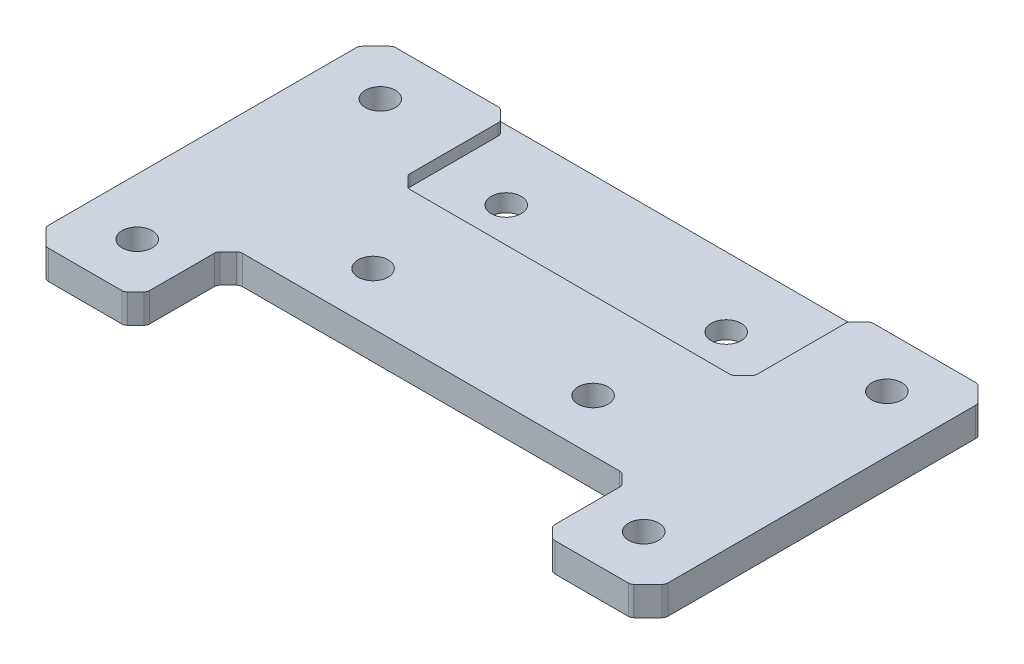
SolidWorks part; units mm, degrees
ref_plane "Front Plane" through (0, 0, 0) normal (0, 0, 1) x (1, 0, 0)
ref_plane "Top Plane" through (0, 0, 0) normal (0, 1, 0) x (1, 0, 0)
ref_plane "Right Plane" through (0, 0, 0) normal (1, 0, 0) x (0, 0, -1)
sketch "Sketch1" plane through (0, 0, 0) normal (0, 1, 0) x (1, 0, 0)
  line L1 (-53.5, -30) -> (53.5, -30)
  line L2 (-53.5, -30) -> (-53.5, 30)
  line L3 (-53.5, 30) -> (53.5, 30)
  line L4 (53.5, -30) -> (53.5, 30)
  line L5 (-53.5, -30) -> (53.5, 30) construction
  line L6 (-53.5, 30) -> (53.5, -30) construction
  point P0 (0, 0)
  dimension "D1" = 107
  dimension "D2" = 60
extrude "Boss-Extrude1" add sketch "Sketch1" along normal blind 5
sketch "Sketch2" plane through (0, 5, 0) normal (0, 1, 0) x (1, 0, 0)
  line L0 (0, 0) -> (0, 37.2033) construction
  line L1 (53.5, 30) -> (-53.5, 30) construction
  line L2 (30, 10) -> (-30, 10)
  line L3 (30, 10) -> (30, 30)
  line L4 (30, 30) -> (-30, 30)
  line L5 (-30, 10) -> (-30, 30)
  line L6 (30, 10) -> (-30, 30) construction
  line L7 (30, 30) -> (-30, 10) construction
  point P3 (0, 20)
  dimension "D1" = 20
  dimension "D2" = 60
extrude "Cut-Extrude1" cut sketch "Sketch2" against normal blind 2
sketch "Sketch3" plane through (0, 5, 0) normal (0, 1, 0) x (1, 0, 0)
  line L0 (0, 0) -> (0, -30) construction
  line L1 (-53.5, -30) -> (53.5, -30) construction
  line L2 (-35, -14) -> (35, -14)
  line L3 (-35, -14) -> (-35, -30)
  line L4 (-35, -30) -> (35, -30)
  line L5 (35, -14) -> (35, -30)
  line L6 (-35, -14) -> (35, -30) construction
  line L7 (-35, -30) -> (35, -14) construction
  line L8 (-30, 10) -> (30, 10) construction
  line L9 (0, 0) -> (0, 32.6833) construction
  point P3 (0, -22)
  dimension "D1" = 70
  dimension "D2" = 24
extrude "Cut-Extrude2" cut sketch "Sketch3" against normal up to next
chamfer "Chamfer1" distance 2 angle 45 8 edges at (30, 4, -30) (30, 4, -10) (-30, 4, -10) (-30, 4, -30) (35, 2.5, 30) (35, 2.5, 14) (-35, 2.5, 14) (-35, 2.5, 30)
chamfer "Chamfer2" distance 3 angle 45 4 edges at (53.5, 2.5, 30) (53.5, 2.5, -30) (-53.5, 2.5, -30) (-53.5, 2.5, 30)
fillet "Fillet1" radius 1 24 edges at (-33, 2.5, 14) (-35, 2.5, 16) (-35, 2.5, 28) (-37, 2.5, 30) (-50.5, 2.5, 30) (-53.5, 2.5, 27) (-53.5, 2.5, -27) (-50.5, 2.5, -30) (-32, 4, -30) (-30, 4, -28) (-30, 4, -12) (-28, 4, -10) (28, 4, -10) (30, 4, -12) (30, 4, -28) (32, 4, -30) (50.5, 2.5, -30) (53.5, 2.5, -27) (53.5, 2.5, 27) (50.5, 2.5, 30) (37, 2.5, 30) (35, 2.5, 28) (35, 2.5, 16) (33, 2.5, 14)
sketch "Sketch4" plane through (0, 5, 0) normal (0, 1, 0) x (1, 0, 0)
  line L0 (0, -38.1823) -> (0, 38.1823) construction
  line L1 (-43.75, 30) -> (-43.75, -30) construction
  line L2 (-32.4142, 30) -> (-50.0858, 30) construction
  line L3 (-50.0858, -30) -> (-37.4142, -30) construction
  line L4 (0, 0) -> (-63.3924, 0) construction
  line L5 (32.5858, -14) -> (-32.5858, -14) construction
  circle A0 centre (-43.75, -21) radius 4.3459
  circle A1 centre (-43.75, 21) radius 4.3459
  circle A2 centre (43.75, -21) radius 4.3459
  circle A3 centre (43.75, 21) radius 4.3459
  circle A4 centre (-19, -5) radius 4.4455
  circle A5 centre (19, -5) radius 4.4455
  point P4 (0, 0)
  dimension "D1" = 43.75
  dimension "D2" = 9
  dimension "D3" = 9
  dimension "D4" = 19
hole_wizard "Tap Drill for M5 Tap1" positions "3DSketch1" profile "Sketch5" hole size "M5" standard "GB"
sketch3d "3DSketch1"
  point P0 (-43.75, 5, -21)
  point P3 (-43.75, 5, 21)
  point P6 (-19, 5, 5)
  point P9 (19, 5, 5)
  point P12 (43.75, 5, -21)
  point P15 (43.75, 5, 21)
sketch "Sketch5" plane through (-43.75, 5, -21) normal (1, 0, 0) x (0, 0, 1)
  line L0 (0, 0) -> (0, 47.5622)
  line L1 (0, 47.5622) -> (2.6, 46)
  line L2 (2.6, 46) -> (2.6, 0)
  line L5 (2.6, 0) -> (0, 0)
  line L10 (0, 47.5622) -> (-2.6, 46) construction
  line L11 (0, -6.35) -> (0, 107.95) construction
  dimension "Hole Dia." = 5.2
  dimension "Hole Depth" = 46
  dimension "Drill Angle" = 118
sketch "Sketch6" plane through (0, 3, 0) normal (0, 1, 0) x (1, 0, 0)
  line L0 (-19, -5) -> (-19, 36.4983) construction
  line L2 (0, 0) -> (0, 34.1088) construction
  line L3 (0, -38.1823) -> (0, 38.1823) construction
  circle A0 centre (-19, 18) radius 3.1659
  circle A1 centre (19, 18) radius 3.1659
  dimension "D1" = 23
hole_wizard "Tap Drill for M5 Tap2" positions "3DSketch2" profile "Sketch7" hole size "M5" standard "GB"
sketch3d "3DSketch2"
  point P0 (-19, 3, -18)
  point P3 (19, 3, -18)
sketch "Sketch7" plane through (-19, 3, -18) normal (1, 0, 0) x (0, 0, 1)
  line L0 (0, 0) -> (0, 47.5622)
  line L1 (0, 47.5622) -> (2.6, 46)
  line L2 (2.6, 46) -> (2.6, 0)
  line L5 (2.6, 0) -> (0, 0)
  line L10 (0, 47.5622) -> (-2.6, 46) construction
  line L11 (0, -6.35) -> (0, 107.95) construction
  dimension "Hole Dia." = 5.2
  dimension "Hole Depth" = 46
  dimension "Drill Angle" = 118
